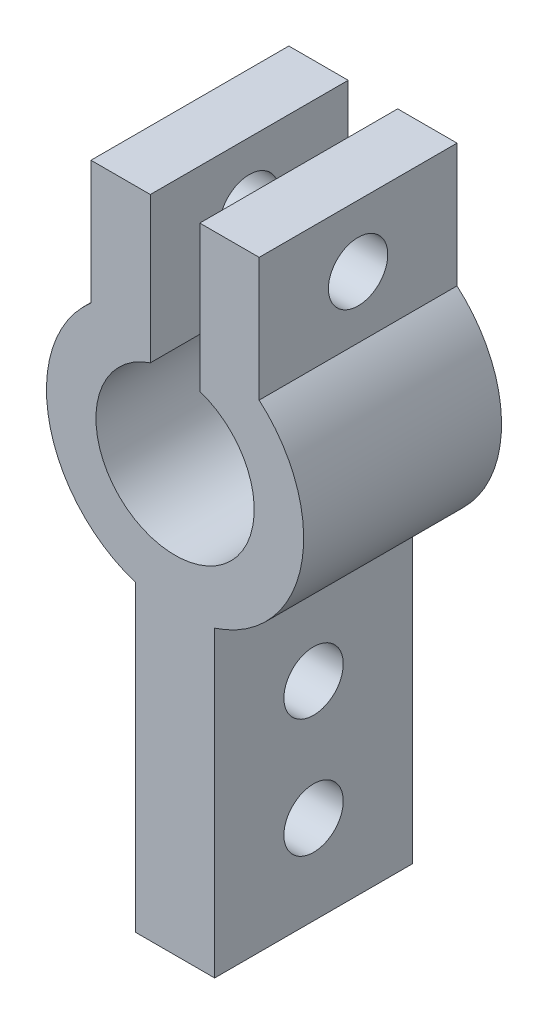
SolidWorks part; units mm, degrees
ref_plane "Front Plane" through (0, 0, 0) normal (0, 0, 1) x (1, 0, 0)
ref_plane "Top Plane" through (0, 0, 0) normal (0, 1, 0) x (1, 0, 0)
ref_plane "Right Plane" through (0, 0, 0) normal (1, 0, 0) x (0, 0, -1)
sketch "Sketch1" plane through (0, 0, 0) normal (0, 0, 1) x (1, 0, 0)
  line L0 (-4.25, 4.9181) -> (-4.25, 11.1681)
  line L1 (-4.25, 11.1681) -> (-1.25, 11.1681)
  line L2 (-1.25, 11.1681) -> (-1.25, 3.7997)
  line L3 (0, 0) -> (0, 6.5) construction
  line L4 (4.25, 11.1681) -> (1.25, 11.1681)
  line L5 (4.25, 4.9181) -> (4.25, 11.1681)
  line L6 (1.25, 11.1681) -> (1.25, 3.7997)
  line L7 (-2, 0) -> (2, 0)
  line L8 (2, 0) -> (2, -21.5)
  line L9 (2, -21.5) -> (-2, -21.5)
  line L10 (-2, -21.5) -> (-2, 0)
  circle A0 centre (0, 0) radius 6.5
  circle A1 centre (0, 0) radius 4
  point P16 (0, 0)
  dimension "D1" = 8
  dimension "D2" = 13
  dimension "D3" = 6.25
  dimension "D4" = 3
  dimension "D5" = 1.25
  dimension "D6" = 4
  dimension "D7" = 21.5
extrude "Boss-Extrude1" add sketch "Sketch1" along normal blind 10 contours A0 L10 L9 L8 | A1 L10 A0 L8 | A1 L2 A0 L10 | A1 L8 A0 L6 | A0 L5 L4 L6 | A0 L2 L1 L0
sketch "Sketch2" plane through (4.25, 0, 0) normal (1, 0, 0) x (0, 0, -1)
  line L0 (-10, 4.9181) -> (0, 11.1681) construction
  line L1 (-5, -21.5) -> (-5, -6.1847) construction
  line L2 (-10, -21.5) -> (0, -21.5) construction
  line L3 (-10, -6.1847) -> (0, -6.1847) construction
  circle A0 centre (-5, 8.0431) radius 1.5
  circle A1 centre (-5, -17) radius 1.5
  circle A2 centre (-5, -11) radius 1.5
  dimension "D1" = 4.5
  dimension "D2" = 6
extrude "Cut-Extrude1" cut sketch "Sketch2" against normal through all both and the other way through all
